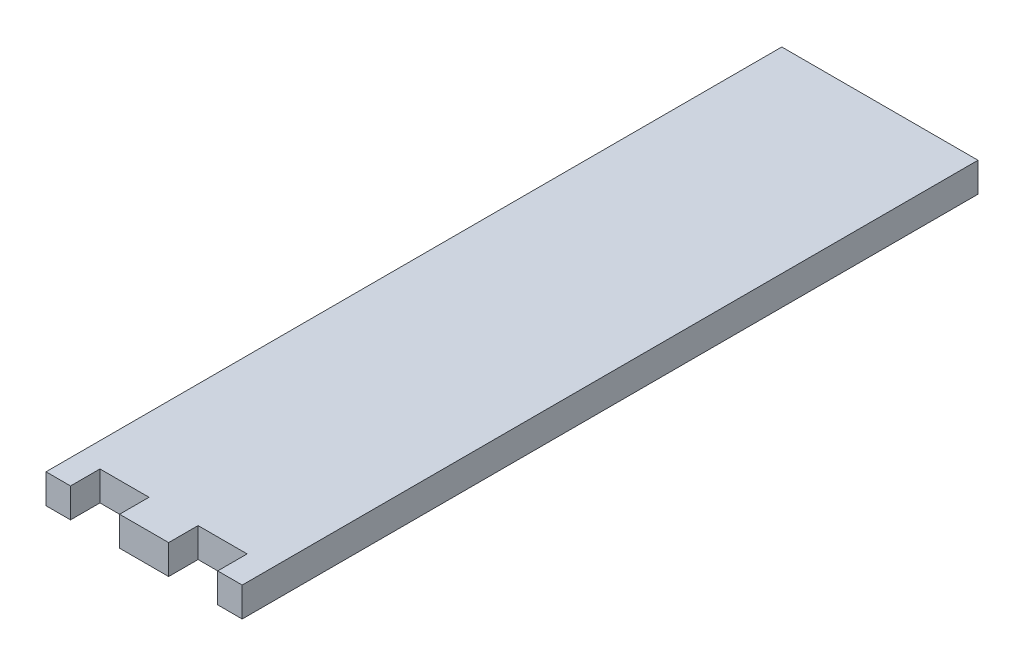
SolidWorks part; units mm, degrees
ref_plane "Front Plane" through (0, 0, 0) normal (0, 0, 1) x (1, 0, 0)
ref_plane "Top Plane" through (0, 0, 0) normal (0, 1, 0) x (1, 0, 0)
ref_plane "Right Plane" through (0, 0, 0) normal (1, 0, 0) x (0, 0, -1)
sketch "Sketch1" plane through (0, 0, 0) normal (0, 1, 0) x (1, 0, 0)
  line L5 (-10, -37.5) -> (10, -37.5)
  line L6 (-10, -37.5) -> (-10, 37.5)
  line L7 (-10, 37.5) -> (10, 37.5)
  line L8 (10, -37.5) -> (10, 37.5)
  line L9 (-10, -37.5) -> (10, 37.5) construction
  line L10 (-10, 37.5) -> (10, -37.5) construction
  point P0 (0, 0)
  dimension "D1" = 20
  dimension "D2" = 75
extrude "Boss-Extrude1" add sketch "Sketch1" along normal blind 3
sketch "Sketch2" plane through (0, 0, 0) normal (0, -1, 0) x (1, 0, 0)
  line L0 (-10, 37.5) -> (10, 37.5) construction
  line L1 (-2.5, 34.5) -> (-7.5, 34.5)
  line L2 (-2.5, 34.5) -> (-2.5, 37.5)
  line L3 (-2.5, 37.5) -> (-7.5, 37.5)
  line L4 (-7.5, 34.5) -> (-7.5, 37.5)
  line L5 (-10, -37.5) -> (-10, 37.5) construction
  dimension "D1" = 3
  dimension "D2" = 5
  dimension "D3" = 2.5
extrude "Cut-Extrude1" cut sketch "Sketch2" against normal through all both and the other way through all
mirror "Mirror1" about plane through (0, 0, 0) normal (1, 0, 0) of "Cut-Extrude1"
